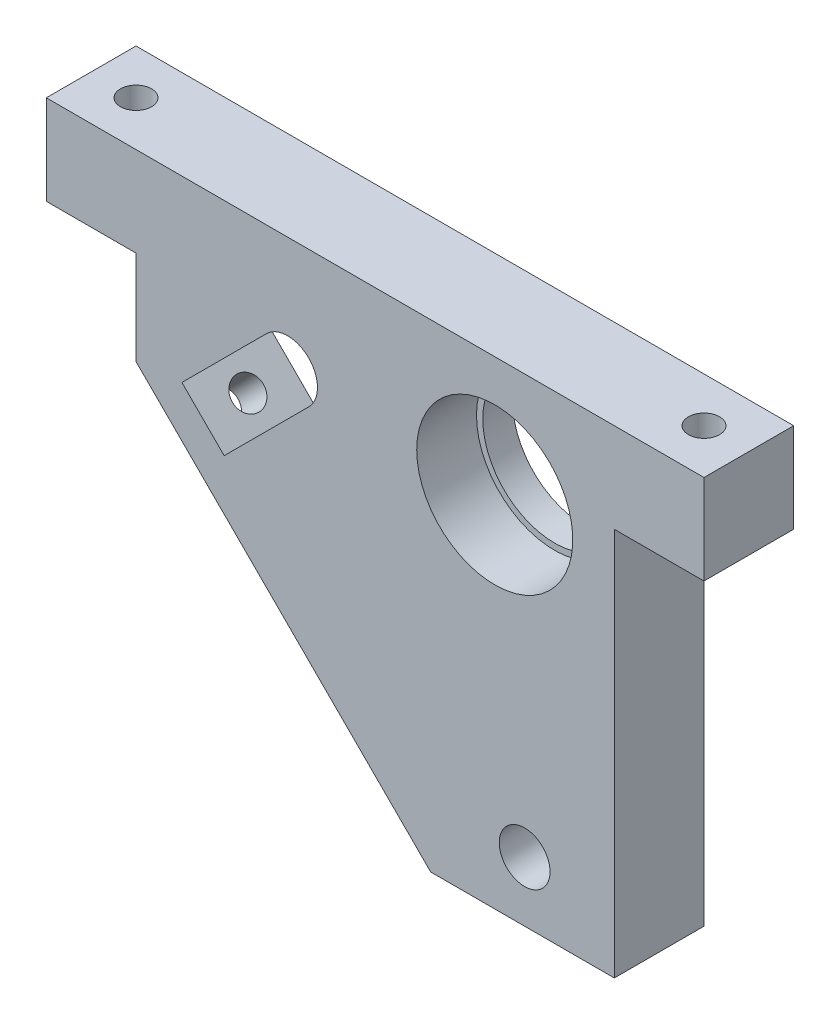
SolidWorks part; units mm, degrees
ref_plane "前视基准面" through (0, 0, 0) normal (0, 0, 1) x (1, 0, 0)
ref_plane "上视基准面" through (0, 0, 0) normal (0, 1, 0) x (1, 0, 0)
ref_plane "右视基准面" through (0, 0, 0) normal (1, 0, 0) x (0, 0, -1)
sketch "草图1" plane through (0, 0, 0) normal (0, 0, 1) x (1, 0, 0)
  line L0 (-33.801, 26.3835) -> (-27.4406, 26.3835)
  line L1 (-33.801, 41.3835) -> (56.199, 41.3835)
  line L2 (-33.801, 41.3835) -> (-33.801, 26.3835)
  line L3 (30.4883, -38.6165) -> (61.199, -38.6165)
  line L5 (-18.801, 10.6728) -> (30.4883, -38.6165)
  line L7 (-28.6333, -13.0935) -> (32.4873, 48.0271) construction
  line L8 (-11.1269, 11.484) -> (3.0152, 25.6261)
  line L9 (6.5876, -28.6165) -> (83.4627, -28.6165) construction
  line L10 (-4.0558, 4.4129) -> (10.0863, 18.5551)
  line L11 (46.199, -4.7233) -> (46.199, -58.0817) construction
  line L12 (-27.4406, 26.3835) -> (-18.801, 26.3835)
  line L13 (-18.801, 26.3835) -> (-18.801, 10.6728)
  line L14 (56.199, 41.3835) -> (76.199, 41.3835)
  line L15 (76.199, 41.3835) -> (76.199, 26.3835)
  line L16 (76.199, 26.3835) -> (61.199, 26.3835)
  line L17 (61.199, 26.3835) -> (61.199, -38.6165)
  line L19 (-11.1269, 11.484) -> (-4.0558, 4.4129)
  circle A0 centre (41.199, 21.3835) radius 12
  circle A1 centre (41.199, 21.3835) radius 25 construction
  arc A3 (10.0863, 18.5551) -> (3.0152, 25.6261) centre (6.5508, 22.0906) ccw
  circle A4 centre (46.199, -28.6165) radius 4.25
  dimension "D3" = 50
  dimension "D4" = 24
  dimension "D5" = 20
  dimension "D6" = 20
  dimension "D8" = 50
  dimension "D13" = 6
  dimension "D14" = 5
  dimension "D15" = 20
  dimension "D17" = 8.5
  dimension "D7" = 45
  dimension "D9" = 15
  dimension "D10" = 15
  dimension "D11" = 45
  dimension "D12" = 25
  dimension "D16" = 10
  dimension "D18" = 15
  dimension "D19" = 15
  dimension "D20" = 15
  dimension "D21" = 110
  dimension "D22" = 80
extrude "凸台-拉伸1" add sketch "草图1" along normal blind 15
sketch "草图2" plane through (0, 0, 15) normal (0, 0, -1) x (-1, 0, 0)
  circle A0 centre (-41.199, 21.3835) radius 13.05
  dimension "D1" = 26.1
extrude "切除-拉伸1" cut sketch "草图2" along normal blind 10
sketch "草图3" plane through (0, 41.3835, 0) normal (0, 1, 0) x (1, 0, 0)
  line L0 (-45.1664, -7.5) -> (87.6779, -7.5) construction
  line L1 (76.199, 0) -> (-33.801, 0) construction
  line L2 (76.199, -15) -> (-33.801, -15) construction
  line L3 (-33.801, -15) -> (-33.801, 0) construction
  line L4 (76.199, -15) -> (76.199, 0) construction
  circle A0 centre (-26.301, -7.5) radius 2.6
  circle A1 centre (68.699, -7.5) radius 2.6
  dimension "D1" = 5.2
  dimension "D2" = 7.5
  dimension "D3" = 7.5
extrude "切除-拉伸2" cut sketch "草图3" against normal through all
sketch "草图5" plane through (-4.0641, -4.0641, 0) normal (-0.7071, -0.7071, 0) x (0, 0, 1)
  line L0 (-9.1574, 10.9911) -> (29.9899, 10.9911) construction
  line L1 (7.5, 30.0407) -> (7.5, -16.3526) construction
  line L2 (0, 20.8411) -> (0, -48.8645) construction
  line L3 (15, 20.8411) -> (15, -48.8645) construction
  line L4 (15, 20.8411) -> (0, 20.8411) construction
  circle A0 centre (7.5, 10.9911) radius 2.6
  dimension "D2" = 5.2
  dimension "D1" = 9.85
extrude "切除-拉伸3" cut sketch "草图5" against normal blind 10
